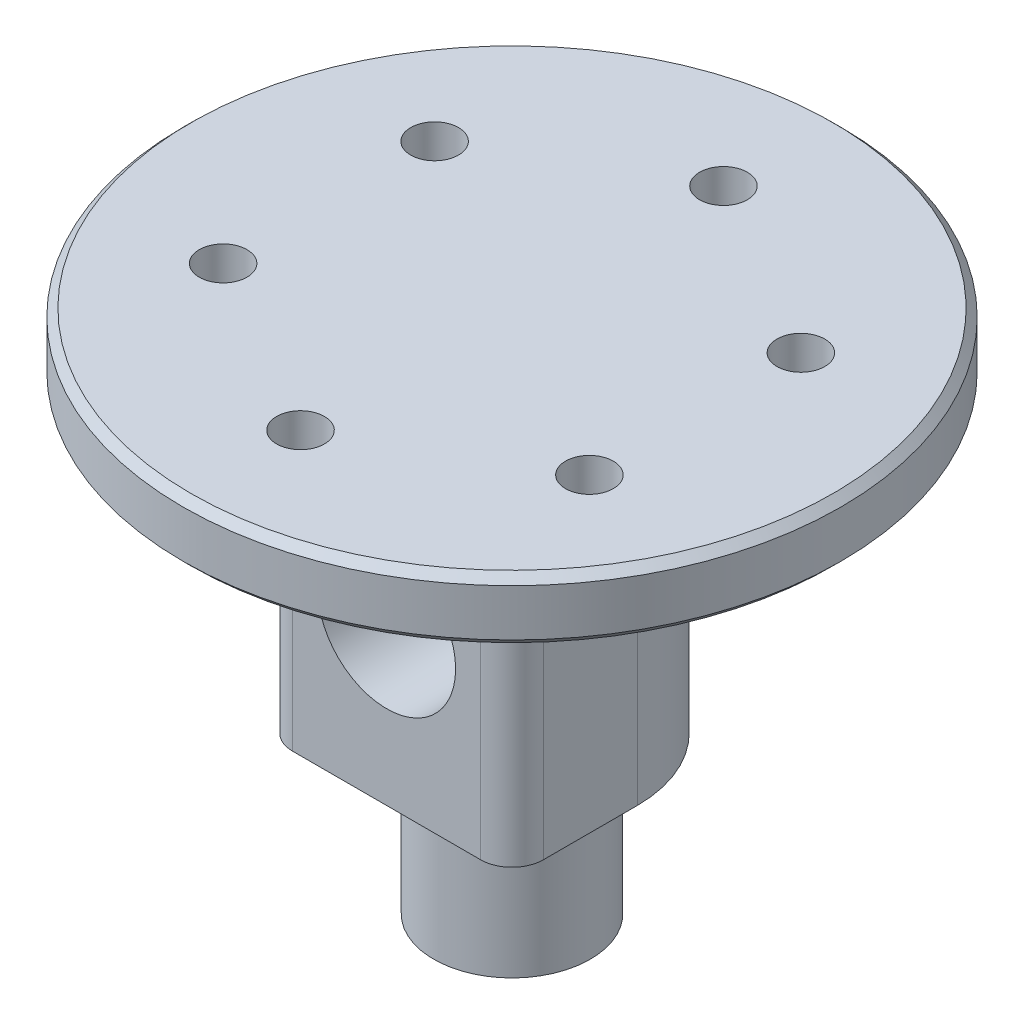
SolidWorks part; units mm, degrees
material "6063-T1"
ref_plane "前视基准面" through (0, 0, 0) normal (0, 0, 1) x (1, 0, 0)
ref_plane "上视基准面" through (0, 0, 0) normal (0, 1, 0) x (1, 0, 0)
ref_plane "右视基准面" through (0, 0, 0) normal (1, 0, 0) x (0, 0, -1)
other "Configuration Table"
sketch "草图1" plane through (0, 0, 0) normal (0, 1, 0) x (1, 0, 0)
  circle A0 centre (0, 0) radius 8
  dimension "D1" = 16
extrude "凸台-拉伸1" add sketch "草图1" along normal blind 19.5
sketch "草图2" plane through (0, 19.5, 0) normal (0, 1, 0) x (1, 0, 0)
  circle A0 centre (0, 0) radius 21
  dimension "D1" = 42
extrude "凸台-拉伸2" add sketch "草图2" along normal blind 4
sketch "草图3" plane through (0, 19.5, 0) normal (0, -1, 0) x (1, 0, 0)
  circle A0 centre (0, 0) radius 13.5 construction
  circle A1 centre (0, -13.5) radius 1.525
  circle A2 centre (-11.6913, -6.75) radius 1.525
  circle A3 centre (-11.6913, 6.75) radius 1.525
  circle A4 centre (0, 13.5) radius 1.525
  circle A5 centre (11.6913, 6.75) radius 1.525
  circle A6 centre (11.6913, -6.75) radius 1.525
  point P17 (0, 0)
  dimension "D1" = 27
  dimension "D2" = 3.05
  dimension "D3" = 6
extrude "切除-拉伸1" cut sketch "草图3" against normal blind 4
sketch "草图5" plane through (0, 0, 0) normal (0, 0, 1) x (1, 0, 0)
  line L0 (-21, 19.5) -> (21, 19.5) construction
  line L1 (-8, 0) -> (8, 0)
  line L2 (-8, 0) -> (-8, 19.5)
  line L3 (-8, 19.5) -> (8, 19.5)
  line L4 (8, 0) -> (8, 19.5)
  line L5 (-8, 0) -> (8, 19.5) construction
  line L6 (-8, 19.5) -> (8, 0) construction
  point P0 (0, 9.75)
  dimension "D1" = 19.5
  dimension "D2" = 9.75
  dimension "D3" = 16
extrude "凸台-拉伸3" add sketch "草图5" along normal blind 8
sketch "草图6" plane through (0, 0, 8) normal (0, 0, 1) x (1, 0, 0)
  line L0 (-8, 19.5) -> (-8, 0) construction
  circle A0 centre (0, 9.75) radius 4.75
  point P4 (-8, 9.75)
  dimension "D1" = 9.5
sketch "草图8" plane through (0, 0, 0) normal (0, -1, 0) x (1, 0, 0)
  circle A0 centre (0, 0) radius 5
  dimension "D1" = 10
extrude "凸台-拉伸4" add sketch "草图8" along normal blind 10
cosmetic thread "装饰螺纹线1" parameters "D1"=10, "D2"=9
sketch "草图9" plane through (0, -10, 0) normal (0, -1, 0) x (1, 0, 0)
  circle A0 centre (0, 0) radius 2.025
  dimension "D1" = 4.05
hole_wizard "G1/8 螺纹孔1" positions "3D草图3" profile "草图12" tap size "G1/8" standard "AS"
sketch3d "3D草图3"
  point P0 (0, 9.75, 8)
cosmetic thread "孔螺蚊线1" parameters "D1"=6, "D2"=9.728
sketch "草图12" plane through (0, 9.75, 8) normal (1, 0, 0) x (0, -1, 0)
  line L0 (0, 0) -> (0, 13.6438)
  line L1 (0, 13.6438) -> (4.4, 11)
  line L2 (4.4, 11) -> (4.4, 0)
  line L5 (4.4, 0) -> (0, 0)
  line L10 (0, 13.6438) -> (-4.4, 11) construction
  line L11 (0, -6.35) -> (0, 107.95) construction
  dimension "螺纹孔钻头直径" = 8.8
  dimension "螺纹孔钻头深度" = 11
  dimension "导头角度" = 118
extrude "切除-拉伸4" cut sketch "草图9" against normal up to surface (15.35 mm away) contours A0
fillet "圆角1" radius 2 2 edges at (8, 9.75, 8) (-8, 9.75, 8)
chamfer "倒角1" distance 0.5 angle 45 2 edges at (0, 23.5, 21) (0, 19.5, 21)
